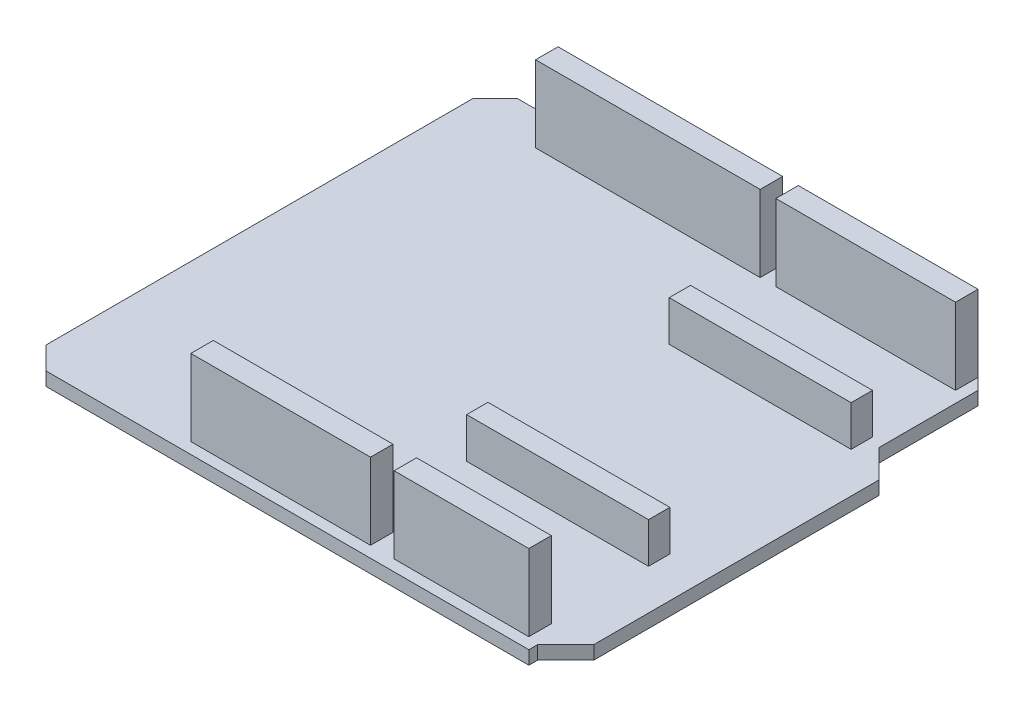
SolidWorks part; units mm, degrees
ref_plane "Front Plane" through (0, 0, 0) normal (0, 0, 1) x (1, 0, 0)
ref_plane "Top Plane" through (0, 0, 0) normal (0, 1, 0) x (1, 0, 0)
ref_plane "Right Plane" through (0, 0, 0) normal (1, 0, 0) x (0, 0, -1)
sketch "Sketch1" plane through (0, 0, 0) normal (0, 1, 0) x (1, 0, 0)
  line L0 (57.15, 39.608) -> (60.325, 36.433)
  line L1 (2.54, 0) -> (57.15, 0)
  line L2 (0, 2.54) -> (0, 50.8)
  line L3 (2.54, 53.34) -> (54.61, 53.34)
  line L4 (57.15, 0) -> (57.15, 1)
  line L5 (60.325, 36.433) -> (60.325, 4.175)
  line L6 (60.325, 4.175) -> (57.15, 1)
  line L7 (57.15, 39.608) -> (57.15, 50.8)
  line L8 (54.61, 53.34) -> (57.15, 50.8)
  line L9 (0, 50.8) -> (2.54, 53.34)
  line L10 (0, 2.54) -> (2.54, 0)
  point P0 (0, 0)
  point P1 (57.15, 53.34)
  point P2 (0, 53.34)
  dimension "D1" = 57.15
  dimension "D2" = 53.34
  dimension "D3" = 60.325
  dimension "D4" = 38.608
  dimension "D5" = 1
extrude "Boss-Extrude1" add sketch "Sketch1" along normal mid plane 1.524
hole_wizard "Ø1.3 (1.3) Diameter Hole1" positions "Sketch2" profile "Sketch3" hole size "Ø1.3" standard "ANSI Metric" end condition up to next
sketch "Sketch2" plane through (0, 0.762, 0) normal (0, 1, 0) x (1, 0, 0)
  line L0 (0, 50.8) -> (0, 2.54) construction
  line L1 (2.54, 0) -> (57.15, 0) construction
  line L2 (18.923, 0) -> (18.923, 2.54) construction
  line L5 (9.652, 50.8) -> (9.652, 53.34) construction
  line L6 (54.61, 53.34) -> (2.54, 53.34) construction
  line L9 (9.652, 50.8) -> (12.192, 50.8) construction
  line L10 (41.91, 2.54) -> (44.45, 2.54) construction
  line L11 (36.83, 50.8) -> (39.37, 50.8) construction
  point P0 (18.923, 2.54)
  point P2 (9.652, 50.8)
  point P25 (21.463, 2.54)
  point P26 (24.003, 2.54)
  point P27 (26.543, 2.54)
  point P28 (29.083, 2.54)
  point P29 (31.623, 2.54)
  point P30 (34.163, 2.54)
  point P31 (36.703, 2.54)
  point P36 (12.192, 50.8)
  point P37 (14.732, 50.8)
  point P38 (17.272, 50.8)
  point P39 (19.812, 50.8)
  point P40 (22.352, 50.8)
  point P41 (24.892, 50.8)
  point P42 (27.432, 50.8)
  point P43 (29.972, 50.8)
  point P44 (32.512, 50.8)
  point P47 (41.91, 2.54)
  point P49 (36.83, 50.8)
  point P56 (44.45, 2.54)
  point P57 (46.99, 2.54)
  point P58 (49.53, 2.54)
  point P59 (52.07, 2.54)
  point P60 (54.61, 2.54)
  point P71 (39.37, 50.8)
  point P72 (41.91, 50.8)
  point P73 (44.45, 50.8)
  point P74 (46.99, 50.8)
  point P75 (49.53, 50.8)
  point P76 (52.07, 50.8)
  point P77 (54.61, 50.8)
  point P194 (91.567, 2.54) [skipped]
  point P196 (89.027, 2.54) [skipped]
  point P198 (86.487, 2.54) [skipped]
  point P200 (83.947, 2.54) [skipped]
  point P202 (81.407, 2.54) [skipped]
  point P204 (78.867, 2.54) [skipped]
  point P205 (76.327, 2.54) [skipped]
  dimension "D1" = 9.652
  dimension "D2" = 50.8
  dimension "D3" = 18.923
  dimension "D5" = 2.54
  dimension "D7" = 2.54
  dimension "D8" = 41.91
  dimension "D10" = 2.54
  dimension "D11" = 36.83
  dimension "D12" = 8
  dimension "D13" = 2.54
  dimension "D4" = 8
  dimension "D6" = 10
  dimension "D9" = 6
sketch "Sketch3" plane through (18.923, 0.762, -2.54) normal (1, 0, 0) x (0, 0, 1)
  line L0 (0, 0) -> (0, 1.524)
  line L1 (0, 1.524) -> (0.65, 1.524)
  line L2 (0.65, 1.524) -> (0.65, 0)
  line L5 (0.65, 0) -> (0, 0)
  line L11 (0, -6.35) -> (0, 107.95) construction
  dimension "Thru Hole Dia." = 1.3
  dimension "Thru Hole Depth" = 1.524
sketch "Sketch6" plane through (0, 0.762, 0) normal (0, 1, 0) x (1, 0, 0)
  line L1 (8.382, 52.07) -> (33.782, 52.07)
  line L2 (8.382, 52.07) -> (8.382, 49.53)
  line L3 (8.382, 49.53) -> (33.782, 49.53)
  line L4 (33.782, 52.07) -> (33.782, 49.53)
  line L5 (35.56, 52.07) -> (55.88, 52.07)
  line L6 (35.56, 52.07) -> (35.56, 49.53)
  line L7 (35.56, 49.53) -> (55.88, 49.53)
  line L8 (55.88, 52.07) -> (55.88, 49.53)
  line L21 (17.653, 3.81) -> (37.973, 3.81)
  line L22 (17.653, 3.81) -> (17.653, 1.27)
  line L23 (17.653, 1.27) -> (37.973, 1.27)
  line L24 (37.973, 3.81) -> (37.973, 1.27)
  line L25 (40.64, 3.81) -> (55.88, 3.81)
  line L26 (40.64, 3.81) -> (40.64, 1.27)
  line L27 (40.64, 1.27) -> (55.88, 1.27)
  line L28 (55.88, 3.81) -> (55.88, 1.27)
  line L33 (32.512, 50.8) -> (33.782, 50.8) construction
  line L34 (9.652, 50.8) -> (8.382, 50.8) construction
  line L35 (36.83, 50.8) -> (35.56, 50.8) construction
  line L36 (54.61, 50.8) -> (55.88, 50.8) construction
  line L42 (18.923, 2.54) -> (17.653, 2.54) construction
  line L43 (36.703, 2.54) -> (37.973, 2.54) construction
  line L44 (40.64, 2.54) -> (41.91, 2.54) construction
  line L45 (54.61, 2.54) -> (55.88, 2.54) construction
  circle A1 centre (54.61, 2.54) radius 0.65 construction
  point P30 (9.652, 50.8)
  point P34 (18.923, 2.54)
  point P43 (54.61, 50.8)
  point P45 (36.83, 50.8)
  point P47 (32.512, 50.8)
  point P69 (41.91, 2.54)
  point P71 (36.703, 2.54)
  dimension "D1" = 2.54
  dimension "D2" = 1.27
extrude "Boss-Extrude2" add sketch "Sketch6" along normal blind 8.636 separate body
sketch "Sketch7" plane through (0, 0.762, 0) normal (0, 1, 0) x (1, 0, 0)
  line L0 (35.56, 49.53) -> (55.88, 49.53) construction
  line L1 (35.179, 40.259) -> (55.753, 40.259)
  line L2 (35.179, 40.259) -> (35.179, 37.846)
  line L3 (35.179, 37.846) -> (55.753, 37.846)
  line L4 (55.753, 40.259) -> (55.753, 37.846)
  line L5 (35.179, 14.933) -> (55.753, 14.933)
  line L6 (35.179, 14.933) -> (35.179, 17.346)
  line L7 (35.179, 17.346) -> (55.753, 17.346)
  line L8 (55.753, 14.933) -> (55.753, 17.346)
  line L9 (0, 50.8) -> (0, 2.54) construction
  dimension "D1" = 2.413
  dimension "D2" = 9.271
  dimension "D3" = 20.5
  dimension "D4" = 20.574
  dimension "D5" = 35.179
extrude "Boss-Extrude3" add sketch "Sketch7" along normal blind 4.572 separate body
